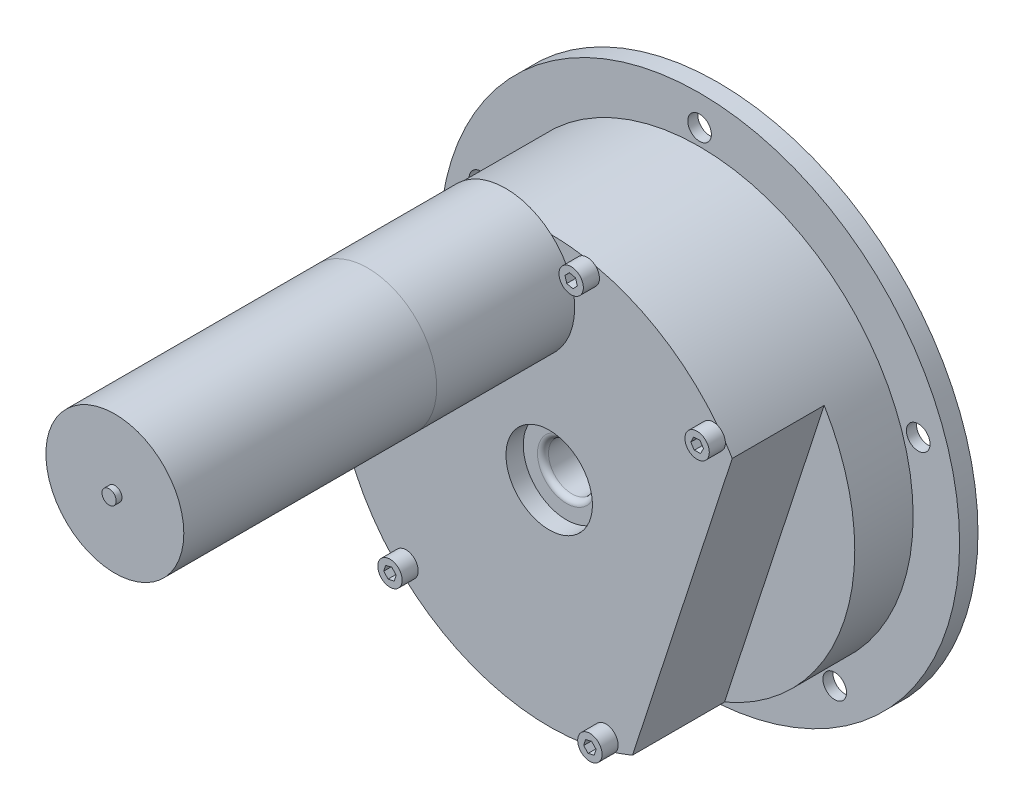
SolidWorks part; units mm, degrees
ref_plane "Front Plane" through (0, 0, 0) normal (0, 0, 1) x (1, 0, 0)
ref_plane "Top Plane" through (0, 0, 0) normal (0, 1, 0) x (1, 0, 0)
ref_plane "Right Plane" through (0, 0, 0) normal (1, 0, 0) x (0, 0, -1)
sketch "Sketch2" plane through (0, 0, 0) normal (1, 0, 0) x (0, 0, -1)
  line L0 (0, 6.477) -> (0, 71.8185)
  line L1 (0, 71.8185) -> (-5.08, 71.8185)
  line L2 (-5.08, 71.8185) -> (-5.08, 58.9915)
  line L3 (-5.08, 58.9915) -> (-46.609, 58.9915)
  line L4 (-46.609, 58.9915) -> (-46.609, 11.938)
  line L5 (-46.609, 0) -> (0, 0) construction
  line L6 (0, 6.477) -> (-41.8465, 6.477)
  line L7 (-46.609, 11.938) -> (-41.8465, 11.938)
  line L8 (-41.8465, 11.938) -> (-41.8465, 6.477)
  dimension "D1" = 71.8185
  dimension "D2" = 58.9915
  dimension "D3" = 5.08
  dimension "D4" = 46.609
  dimension "D5" = 6.477
  dimension "D6" = 4.7625
  dimension "D7" = 11.938
revolve "Revolve1" add sketch "Sketch2" angle 360 about L5
fillet "Fillet1" radius 1.524 1 edges at (6.477, 0, 41.8465)
sketch "Sketch3" plane through (0, 0, 0) normal (0, 0, -1) x (-1, 0, 0)
  circle A0 centre (0, 0) radius 56.007
  dimension "D1" = 112.014
extrude "Extrude1" cut sketch "Sketch3" against normal blind 2.6416
sketch "Sketch4" plane through (0, 0, 2.6416) normal (0, 0, -1) x (-1, 0, 0)
  circle A0 centre (0, 0) radius 40.005
  circle A1 centre (0, 0) radius 6.477
  circle A2 centre (0, 0) radius 6.477 construction
  dimension "D1" = 80.01
extrude "Extrude2" [suppressed] add sketch "Sketch4" along normal blind 3.429
fillet "Fillet2" [suppressed] radius 3.175
sketch "Sketch5" plane through (0, 0, 5.08) normal (0, 0, 1) x (1, 0, 0)
  circle A0 centre (0, 63.5) radius 3.2639
  circle A1 centre (0, 0) radius 6.477 construction
  circle A2 centre (60.3921, 19.6226) radius 3.2639
  circle A3 centre (37.3244, -51.3726) radius 3.2639
  circle A4 centre (-37.3244, -51.3726) radius 3.2639
  circle A5 centre (-60.3921, 19.6226) radius 3.2639
  dimension "D1" = 6.5278
  dimension "D2" = 63.5
extrude "Extrude3" cut sketch "Sketch5" against normal up to next
chamfer "Chamfer1" distance 3.9878 angle 30 5 edges at (40.5883, -51.3726, 0) (-34.0605, -51.3726, 0) (-57.1282, 19.6226, 0) (3.2639, 63.5, 0) (63.656, 19.6226, 0)
sketch "Sketch6" plane through (0, 0, 46.609) normal (0, 0, 1) x (1, 0, 0)
  line L0 (60.3921, 19.6226) -> (37.3244, -51.3726) construction
  line L1 (50.5456, 30.4162) -> (23.0141, -54.3171)
  line L2 (23.0141, -54.3171) -> (47.1709, -62.1662)
  line L3 (47.1709, -62.1662) -> (74.7024, 22.5671)
  line L4 (74.7024, 22.5671) -> (50.5456, 30.4162)
  circle A0 centre (0, 0) radius 58.9915 construction
  circle A1 centre (0, 0) radius 58.9915 construction
  dimension "D1" = 12.7
  dimension "D2" = 25.4
extrude "Extrude4" cut sketch "Sketch6" against normal blind 25.4
sketch "Sketch7" plane through (0, 0, 46.609) normal (0, 0, 1) x (1, 0, 0)
  line L0 (0, 0) -> (-12.0238, 44.7027) construction
  line L1 (-12.0238, 44.7027) -> (-16.9719, 63.0989) construction
  circle A0 centre (-12.0238, 44.7027) radius 19.05
  circle A2 centre (0, 63.5) radius 3.2639 construction
  dimension "D1" = 38.1
  dimension "D2" = 65.3415
extrude "Extrude5" add sketch "Sketch7" along normal blind 107.95
sketch "Sketch8" plane through (0, 0, 0) normal (1, 0, 0) x (0, 0, -1)
  line L0 (-46.609, 63.7527) -> (-46.609, 17.3527)
  line L1 (-46.609, 50.7392) -> (-46.609, -58.9915) construction
  line L2 (-46.609, 17.3527) -> (-84.709, 17.3527)
  line L3 (-84.709, 17.3527) -> (-84.709, 70.0339)
  dimension "D1" = 38.1
split line "Split Line1"
sketch "Sketch9" plane through (0, 0, 46.609) normal (0, 0, 1) x (1, 0, 0)
  line L0 (12.2159, 54.7311) -> (11.7165, 56.4185)
  line L1 (46.2606, 31.6965) -> (47.0462, 33.2712)
  line L2 (47.0462, 33.2712) -> (46.0753, 34.7389)
  line L3 (46.0753, 34.7389) -> (44.3188, 34.6319)
  line L4 (44.3188, 34.6319) -> (43.5332, 33.0572)
  line L5 (43.5332, 33.0572) -> (44.5041, 31.5896)
  line L6 (44.5041, 31.5896) -> (46.2606, 31.6965)
  line L7 (11.7165, 56.4185) -> (10.0055, 56.8297)
  line L8 (10.0055, 56.8297) -> (8.7938, 55.5536)
  line L9 (8.7938, 55.5536) -> (9.2932, 53.8661)
  line L10 (9.2932, 53.8661) -> (11.0042, 53.4549)
  line L11 (11.0042, 53.4549) -> (12.2159, 54.7311)
  line L12 (13.9629, -54.3116) -> (15.1739, -55.5884)
  line L13 (15.1739, -55.5884) -> (16.8852, -55.1781)
  line L14 (16.8852, -55.1781) -> (17.3854, -53.4909)
  line L15 (17.3854, -53.4909) -> (16.1744, -52.2141)
  line L16 (16.1744, -52.2141) -> (14.4632, -52.6245)
  line L17 (14.4632, -52.6245) -> (13.9629, -54.3116)
  line L18 (-55.8118, 5.4548) -> (-57.4258, 4.7535)
  line L19 (-57.4258, 4.7535) -> (-57.6255, 3.0051)
  line L20 (-57.6255, 3.0051) -> (-56.2112, 1.958)
  line L21 (-56.2112, 1.958) -> (-54.5972, 2.6593)
  line L22 (-54.5972, 2.6593) -> (-54.3975, 4.4077)
  line L23 (-54.3975, 4.4077) -> (-55.8118, 5.4548)
  line L24 (45.2897, 33.1642) -> (0, 0) construction
  line L25 (0, 0) -> (17.3854, -23.7419) construction
  line L26 (-40.7327, -38.5431) -> (-41.2623, -40.2212)
  line L27 (-41.2623, -40.2212) -> (-40.0737, -41.519)
  line L28 (-40.0737, -41.519) -> (-38.3556, -41.1385)
  line L29 (-38.3556, -41.1385) -> (-37.826, -39.4604)
  line L30 (-37.826, -39.4604) -> (-39.0145, -38.1626)
  line L31 (-39.0145, -38.1626) -> (-40.7327, -38.5431)
  circle A0 centre (45.2897, 33.1642) radius 3.3655
  circle A1 centre (45.2897, 33.1642) radius 1.524 construction
  arc A2 (50.5456, 30.4162) -> (0.5783, 58.9887) centre (0, 0) ccw construction
  circle A3 centre (10.5049, 55.1423) radius 3.3655
  circle A4 centre (10.5049, 55.1423) radius 1.524 construction
  circle A5 centre (15.6742, -53.9013) radius 3.3655
  circle A6 centre (15.6742, -53.9013) radius 1.524 construction
  circle A7 centre (-56.0115, 3.7064) radius 3.3655
  circle A8 centre (-56.0115, 3.7064) radius 1.524 construction
  circle A9 centre (-39.5441, -39.8408) radius 3.3655
  circle A10 centre (-39.5441, -39.8408) radius 1.524 construction
  dimension "D1" = 6.731
  dimension "D4" = 56.134
  dimension "D2" = 3.048
  dimension "D3" = 5.9309
extrude "Extrude6" add sketch "Sketch9" along normal blind 4.445
sketch "Sketch10" plane through (0, 0, 154.559) normal (0, 0, 1) x (1, 0, 0)
  circle A0 centre (-12.0238, 44.7027) radius 1.9685
  circle A1 centre (-12.0238, 44.7027) radius 19.05 construction
  dimension "D1" = 3.937
extrude "Extrude7" add sketch "Sketch10" along normal blind 24.765
hole_wizard "M6x1.0 Tapped Hole1" [suppressed] positions "3DSketch2" profile "Sketch13" tap size "M6x1.0" standard "ANSI Metric"
sketch3d "3DSketch2" [suppressed]
  point P0 (-0.1657, 35.4239, -0.7874)
  dimension "D1" = 35.433
sketch "Sketch13" plane through (-0.1657, 35.4239, -0.7874) normal (1, 0, 0) x (0, 1, 0)
  line L0 (0, 0) -> (0, 13.1862)
  line L1 (0, 13.1862) -> (2.5, 11.684)
  line L2 (2.5, 11.684) -> (2.5, 0)
  line L5 (2.5, 0) -> (0, 0)
  line L10 (0, 13.1862) -> (-2.5, 11.684) construction
  line L11 (0, -6.35) -> (0, 107.95) construction
  dimension "Tap Drill Dia." = 5
  dimension "Tap Drill Depth" = 11.684
  dimension "Drill Angle" = 118
cosmetic thread "Hole Thread1" [suppressed] parameters "D1"=0, "D2"=6
pattern_circular "CirPattern1" [suppressed] count 4 over 360
sketch "Sketch14" plane through (0, 0, 0) normal (0, 0, -1) x (-1, 0, 0)
  circle A0 centre (0, 0) radius 63.5 construction
sketch "Sketch15" plane through (0, 0, 154.559) normal (0, 0, 1) x (1, 0, 0)
  circle A0 centre (-12.0238, 44.7027) radius 1.9685
  circle A1 centre (-12.0238, 44.7027) radius 1.9685 construction
extrude "Cut-Extrude1" cut sketch "Sketch15" along normal through all from offset 1.5875
